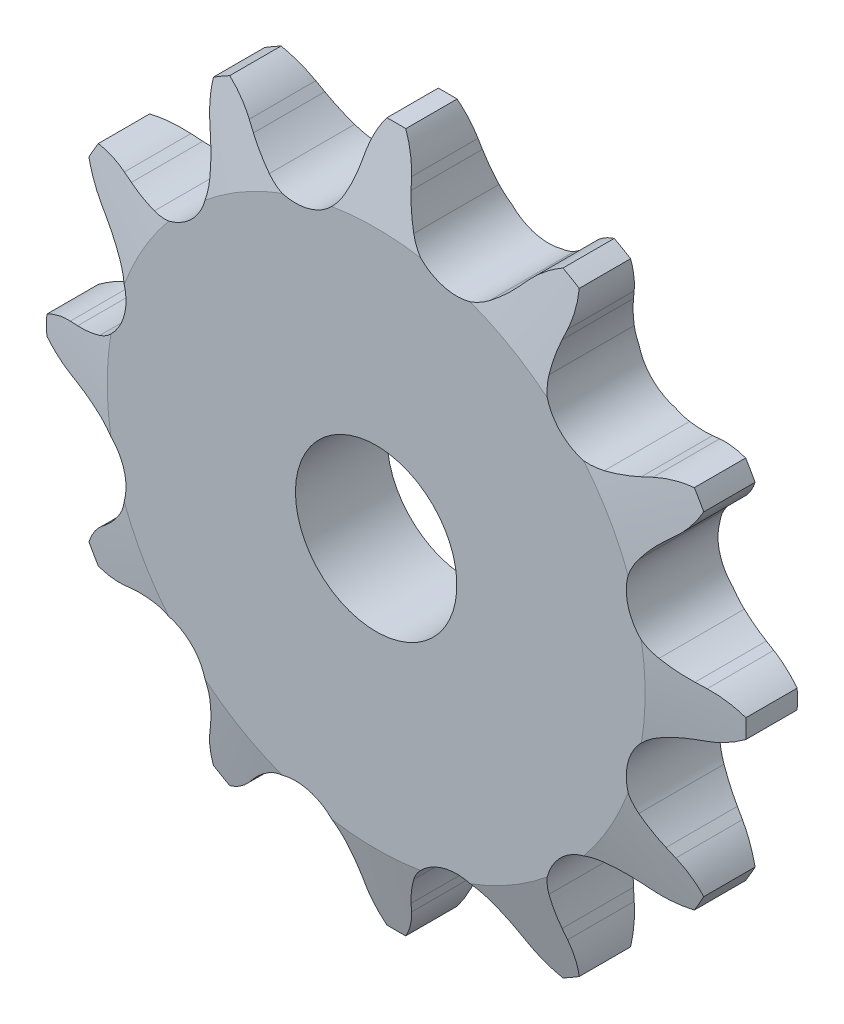
SolidWorks part; units mm, degrees
ref_plane "Front Plane" through (0, 0, 0) normal (0, 0, 1) x (1, 0, 0)
ref_plane "Top Plane" through (0, 0, 0) normal (0, 1, 0) x (1, 0, 0)
ref_plane "Right Plane" through (0, 0, 0) normal (1, 0, 0) x (0, 0, -1)
sketch "Sketch0" plane through (0, 0, 0) normal (0, 0, 1) x (1, 0, 0)
  line L0 (6.35, -23.6985) -> (0, 0) construction
  line L1 (0, 0) -> (17.3485, -17.3485) construction
  line L2 (0, 0) -> (-6.35, -23.6985) construction
  line L3 (6.35, -23.6985) -> (17.3485, -17.3485) construction
  line L4 (6.35, -23.6985) -> (-6.35, -23.6985) construction
  line L5 (10.9724, -22.5882) -> (10.4529, -22.0044)
  line L6 (6.35, -23.6985) -> (0, -25.4) construction
  line L7 (1.7917, -25.0482) -> (1.9497, -24.2829)
  line L8 (0, -23.6985) -> (0, -27.5085) construction
  line L9 (8.656, -20.4053) -> (2.7136, -28.8918) construction
  line L10 (0, 0) -> (0, -23.6985) construction
  line L11 (10.4529, -22.0044) -> (2.7136, -28.8918) construction
  line L12 (0, -27.5085) -> (0, -28.3926) construction
  line L13 (15.9583, -18.1512) -> (10.9724, -22.5882) construction
  circle A0 centre (0, 0) radius 27.5085 construction
  circle A1 centre (0, 0) radius 24.5345 construction
  arc A2 (-6.055, -30.243) -> (20.3653, -23.1637) centre (0, 0) ccw
  circle A3 centre (0, 0) radius 28.3926 construction
  circle A4 centre (6.35, -23.6985) radius 3.9624 construction
  arc A7 (8.656, -20.4053) -> (2.7064, -21.9995) centre (6.35, -23.6985) ccw
  circle A8 centre (6.35, -23.6985) radius 4.0203 construction
  arc A9 (10.9724, -22.5882) -> (20.3653, -23.1637) centre (15.9583, -18.1512) ccw
  arc A10 (10.4529, -22.0044) -> (8.656, -20.4053) centre (2.7136, -28.8918) ccw
  arc A11 (1.7917, -25.0482) -> (-6.055, -30.243) centre (-4.7447, -23.6985) cw
  arc A12 (1.9497, -24.2829) -> (2.7064, -21.9995) centre (12.0958, -26.3779) cw
  dimension "D1" = 4.0203
  dimension "Dr" = 7.9248
  dimension "Ds" = 8.0406
  dimension "R" = 4.0203
  dimension "Pitch" = 12.7
  dimension "A" = 40
  dimension "360/N" = 30
  dimension "B" = 13.333
  dimension "ab" = 11.0947
  dimension "J" = 3.81
  dimension "ac" = 6.3398
sketch "Sketch1" plane through (0, 0, 0) normal (1, 0, 0) x (0, 0, -1)
  line L0 (3.6068, 0) -> (-3.6068, 0)
  line L1 (-3.6068, 0) -> (-3.6068, 21.1585)
  line L2 (-3.6068, 21.1585) -> (-2.0193, 27.5085)
  line L3 (-2.0193, 27.5085) -> (2.0193, 27.5085)
  line L4 (2.0193, 27.5085) -> (3.6068, 21.1585)
  line L5 (3.6068, 21.1585) -> (3.6068, 0)
  line L7 (0, 27.5085) -> (0, 0) construction
  line L8 (-3.6068, 21.1585) -> (3.6068, 21.1585) construction
  line L9 (0, 27.5085) -> (0, -27.5085) construction
  line L10 (-3.6068, 21.1585) -> (-3.6068, 27.5085) construction
  line L11 (-3.6068, 27.5085) -> (-2.0193, 27.5085) construction
  line L12 (2.0193, 27.5085) -> (3.6068, 27.5085) construction
  line L13 (3.6068, 27.5085) -> (3.6068, 21.1585) construction
  dimension "t" = 7.2136
  dimension "g" = 1.5875
  dimension "h" = 6.35
revolve "Revolve1" add sketch "Sketch1" angle 360 mid plane about L0
extrude "Cut-Extrude1" cut sketch "Sketch0" against normal through all and the other way through all
pattern_circular "CirPattern1" count 12 over 360 about axis through (0, 0, 0) along (0, 0, 1) of "Cut-Extrude1"
sketch "Sketch2" plane through (0, 0, 0) normal (0, 0, 1) x (1, 0, 0)
  circle A0 centre (0, 0) radius 6.35 construction
  circle A1 centre (0, 0) radius 30.1625
  circle A2 centre (0, 0) radius 27.559 construction
  dimension "Bore" = 12.7
  dimension "Hub Dia." = 60.325
  dimension "OD" = 55.118
sketch "Sketch3" plane through (0, 0, 0) normal (0, 0, 1) x (1, 0, 0)
  circle A0 centre (0, 0) radius 6.35 construction
  circle A1 centre (0, 0) radius 6.35
  circle A2 centre (0, 0) radius 27.559 construction
  circle A3 centre (0, 0) radius 27.559
extrude "Cut-Extrude2" cut sketch "Sketch3" along normal through all and the other way through all flip side to cut
equation "\"360/N@Sketch0\" = 360/\"Teeth@CirPattern1\""
equation "\"Ds@Sketch0\" = 1.005 * \"Dr@Sketch0\" + 0.003"
equation "\"R@Sketch0\" = 1/2 * \"Ds@Sketch0\""
equation "\"A@Sketch0\" = 35 +  ( 60 / \"Teeth@CirPattern1\" ) "
equation "\"B@Sketch0\" = 18 -  ( 56 / \"Teeth@CirPattern1\" )"
equation "\"ac@Sketch0\" = 0.8 * \"Dr@Sketch0\""
equation "\"ab@Sketch0\" = 1.4 * \"Dr@Sketch0\""
equation "\"J@Sketch0\" = 0.3 * \"Pitch@Sketch0\""
equation "\"h@Sketch1\" = \"Pitch@Sketch0\" / 2"
equation "\"g@Sketch1\" = \"h@Sketch1\" / 4"
